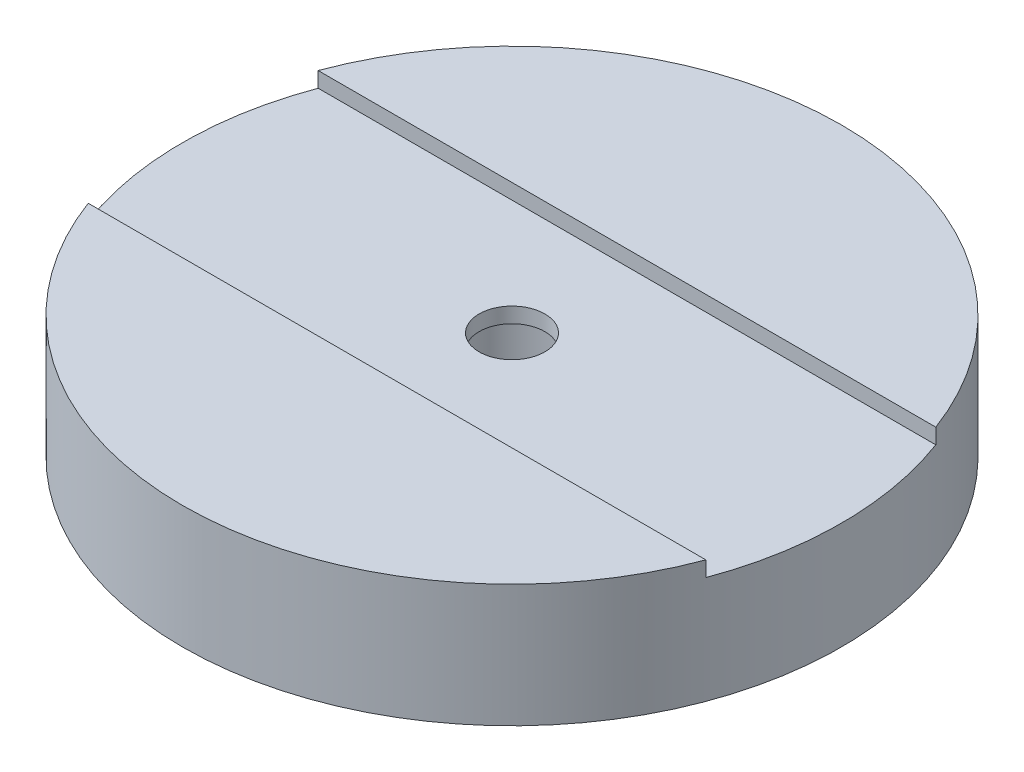
SolidWorks part; units mm, degrees
ref_plane "Front Plane" through (0, 0, 0) normal (0, 0, 1) x (1, 0, 0)
ref_plane "Top Plane" through (0, 0, 0) normal (0, 1, 0) x (1, 0, 0)
ref_plane "Right Plane" through (0, 0, 0) normal (1, 0, 0) x (0, 0, -1)
sketch "Sketch1" plane through (0, 0, 0) normal (0, 1, 0) x (1, 0, 0)
  circle A0 centre (0, 0) radius 3.935
  circle A1 centre (0, 0) radius 21.5
  dimension "D1" = 7.87
  dimension "D2" = 43
extrude "Boss-Extrude1" add sketch "Sketch1" along normal blind 6
sketch "Sketch2" plane through (0, 6, 0) normal (0, 1, 0) x (1, 0, 0)
  circle A0 centre (0, 0) radius 21.5
  circle A1 centre (0, 0) radius 2.1462
  circle A2 centre (0, 0) radius 21.5 construction
extrude "Boss-Extrude2" add sketch "Sketch2" along normal blind 2
sketch "Sketch3" plane through (0, 8, 0) normal (0, 1, 0) x (1, 0, 0)
  line L1 (23.9897, 7.5) -> (-23.9897, 7.5)
  line L2 (23.9897, 7.5) -> (23.9897, -7.5)
  line L3 (23.9897, -7.5) -> (-23.9897, -7.5)
  line L4 (-23.9897, 7.5) -> (-23.9897, -7.5)
  line L5 (23.9897, 7.5) -> (-23.9897, -7.5) construction
  line L6 (23.9897, -7.5) -> (-23.9897, 7.5) construction
  point P0 (0, 0)
  dimension "D1" = 15
extrude "Cut-Extrude1" cut sketch "Sketch3" against normal blind 1
